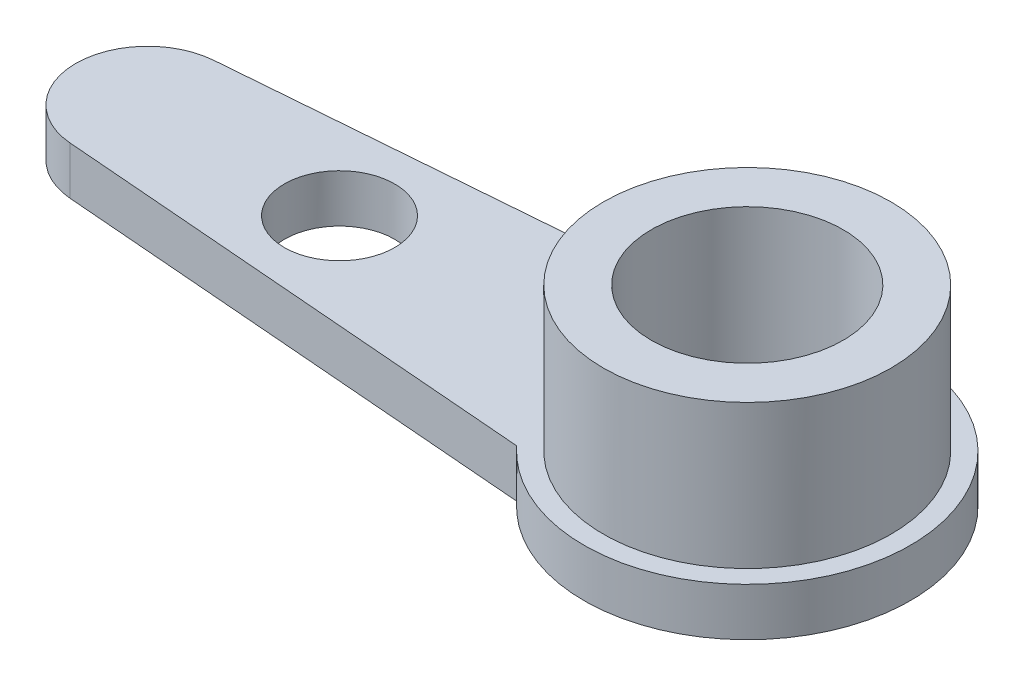
SolidWorks part; units mm, degrees
material "uhlíková ocel 7850"
ref_plane "Přední rovina" through (0, 0, 0) normal (0, 0, 1) x (1, 0, 0)
ref_plane "Horní rovina" through (0, 0, 0) normal (0, 1, 0) x (1, 0, 0)
ref_plane "Pravá rovina" through (0, 0, 0) normal (1, 0, 0) x (0, 0, -1)
sketch "Skica1" plane through (0, 0, 0) normal (0, 1, 0) x (1, 0, 0)
  line L0 (0, 0) -> (-12.5, 0) construction
  line L1 (-12.62, 1.4952) -> (-2.5, 2.3074)
  line L2 (0, 15.429) -> (0, 0) construction
  line L3 (-12.5, 0) -> (-39.2821, 0) construction
  line L4 (12.62, 1.4952) -> (2.5, 2.3074)
  line L5 (12.62, -1.4952) -> (2.5, -2.3074)
  line L6 (-12.62, -1.4952) -> (-2.5, -2.3074)
  line L7 (0, 2.5) -> (-5.8693, 2.5) construction
  line L8 (-2.5, 2.3074) -> (-2.5, 5.25)
  line L9 (2.5, 2.3074) -> (2.5, 5.25)
  line L10 (2.5, -2.3074) -> (2.5, -5.25)
  line L11 (-2.5, -2.3074) -> (-2.5, -5.25)
  circle A0 centre (0, 0) radius 2
  arc A1 (2.5, -5.25) -> (-2.5, -5.25) centre (0, -5.25) cw
  arc A2 (-12.62, 1.4952) -> (-12.62, -1.4952) centre (-12.5, 0) ccw
  arc A3 (12.62, 1.4952) -> (12.62, -1.4952) centre (12.5, 0) cw
  arc A5 (2.5, 5.25) -> (-2.5, 5.25) centre (0, 5.25) ccw
  point P19 (0, 7.75)
  dimension "D1" = 4
  dimension "D2" = 1.5
  dimension "D3" = 2.5
  dimension "D5" = 15.5
  dimension "D7" = 2.5
  dimension "D4" = 12.5
  dimension "D6" = 5
extrude "Přidat vysunutím1" add sketch "Skica1" along normal blind 1
sketch "Skica2" plane through (0, 1, 0) normal (0, 1, 0) x (1, 0, 0)
  line L0 (-8.5, 0) -> (0, 0) construction
  line L1 (0, 0) -> (0, -4.2214) construction
  line L2 (0, 0) -> (8.5, 0) construction
  circle A0 centre (-8.5, 0) radius 1.15
  circle A1 centre (8.5, 0) radius 1.15
  dimension "D1" = 2.3
  dimension "D2" = 17
extrude "Odebrat vysunutím1" cut sketch "Skica2" against normal blind 2
sketch "Skica3" plane through (0, 1, 0) normal (0, 1, 0) x (1, 0, 0)
  circle A1 centre (0, 0) radius 3
  circle A2 centre (0, 0) radius 2
  circle A3 centre (0, 0) radius 2 construction
  dimension "D1" = 6
extrude "Přidat vysunutím2" add sketch "Skica3" along normal blind 3
sketch "Skica4" plane through (0, 0, 0) normal (0, -1, 0) x (1, 0, 0)
  line L1 (-2.5, 2.3074) -> (-2.5, 10.5881)
  line L2 (-2.5, 10.5881) -> (18.0051, 10.5881)
  line L3 (18.0051, 10.5881) -> (18.0051, -8.7177)
  line L4 (18.0051, -8.7177) -> (-2.5, -8.8682)
  line L5 (-2.5, -8.8682) -> (-2.5, -2.3074)
  arc A0 (-2.5, -2.3074) -> (-2.5, 2.3074) centre (0, 0) ccw
extrude "Odebrat vysunutím2" cut sketch "Skica4" against normal blind 10
